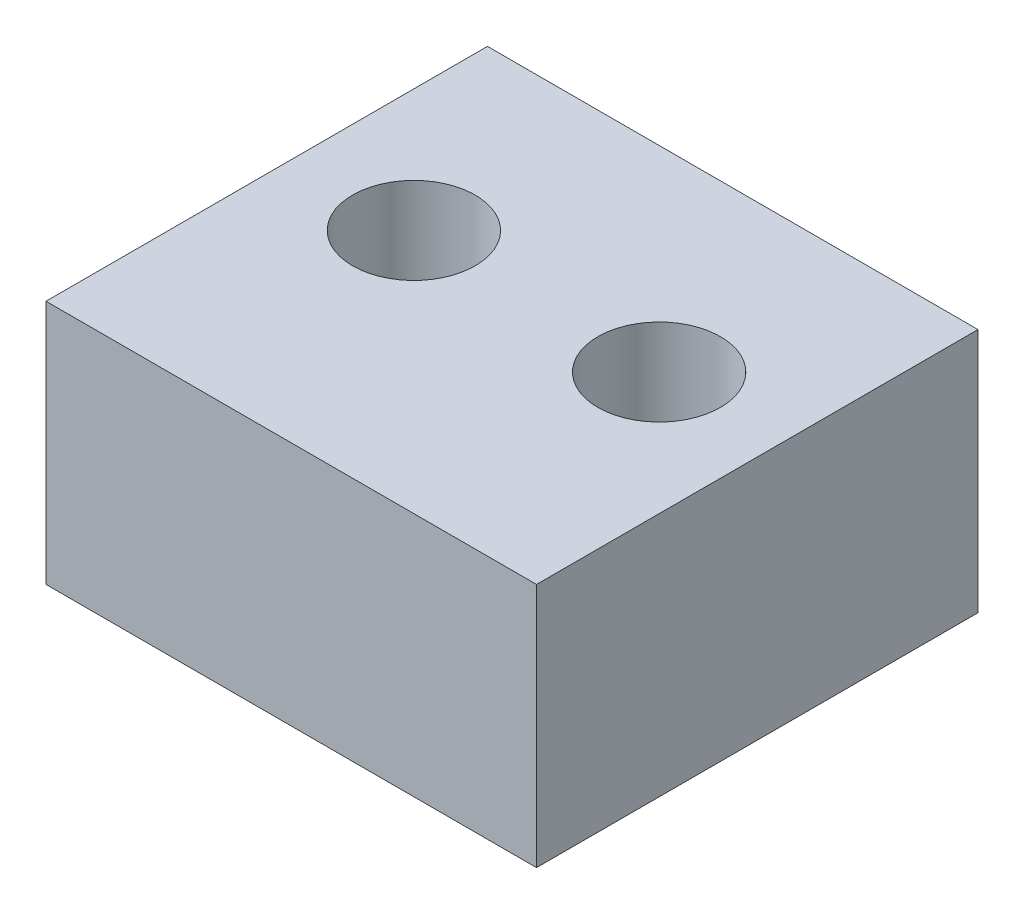
SolidWorks part; units mm, degrees
ref_plane "Front Plane" through (0, 0, 0) normal (0, 0, 1) x (1, 0, 0)
ref_plane "Top Plane" through (0, 0, 0) normal (0, 1, 0) x (1, 0, 0)
ref_plane "Right Plane" through (0, 0, 0) normal (1, 0, 0) x (0, 0, -1)
sketch "Sketch1" plane through (0, 0, 0) normal (0, 1, 0) x (1, 0, 0)
  line L1 (-12.7, 11.43) -> (12.7, 11.43)
  line L2 (-12.7, 11.43) -> (-12.7, -11.43)
  line L3 (-12.7, -11.43) -> (12.7, -11.43)
  line L4 (12.7, 11.43) -> (12.7, -11.43)
  line L5 (-12.7, 11.43) -> (12.7, -11.43) construction
  line L6 (-12.7, -11.43) -> (12.7, 11.43) construction
  point P0 (0, 0)
extrude "Boss-Extrude1" add sketch "Sketch1" along normal blind 12.7
sketch "Sketch2" plane through (0, 12.7, 0) normal (0, 1, 0) x (1, 0, 0)
  line L0 (-12.7, 11.43) -> (-12.7, 1.27)
  line L1 (-12.7, 11.43) -> (-12.7, -11.43) construction
  line L2 (-12.7, 1.27) -> (-6.35, 1.27)
  line L3 (12.7, 11.43) -> (12.7, 1.27)
  line L4 (12.7, -11.43) -> (12.7, 11.43) construction
  line L5 (12.7, 1.27) -> (6.35, 1.27)
hole_wizard "1/4 (0.25) Diameter Hole1" positions "Sketch3" profile "Sketch4" hole size "1/4" standard "ANSI Inch" end condition up to next
sketch "Sketch3" plane through (0, 12.7, 0) normal (0, 1, 0) x (1, 0, 0)
  point P0 (-6.35, 1.27)
  point P3 (6.35, 1.27)
sketch "Sketch4" plane through (-6.35, 12.7, -1.27) normal (1, 0, 0) x (0, 0, 1)
  line L0 (0, 0) -> (0, 12.7)
  line L1 (0, 12.7) -> (3.175, 12.7)
  line L2 (3.175, 12.7) -> (3.175, 0)
  line L5 (3.175, 0) -> (0, 0)
  line L11 (0, -6.35) -> (0, 107.95) construction
  dimension "Thru Hole Dia." = 6.35
  dimension "Thru Hole Depth" = 12.7
